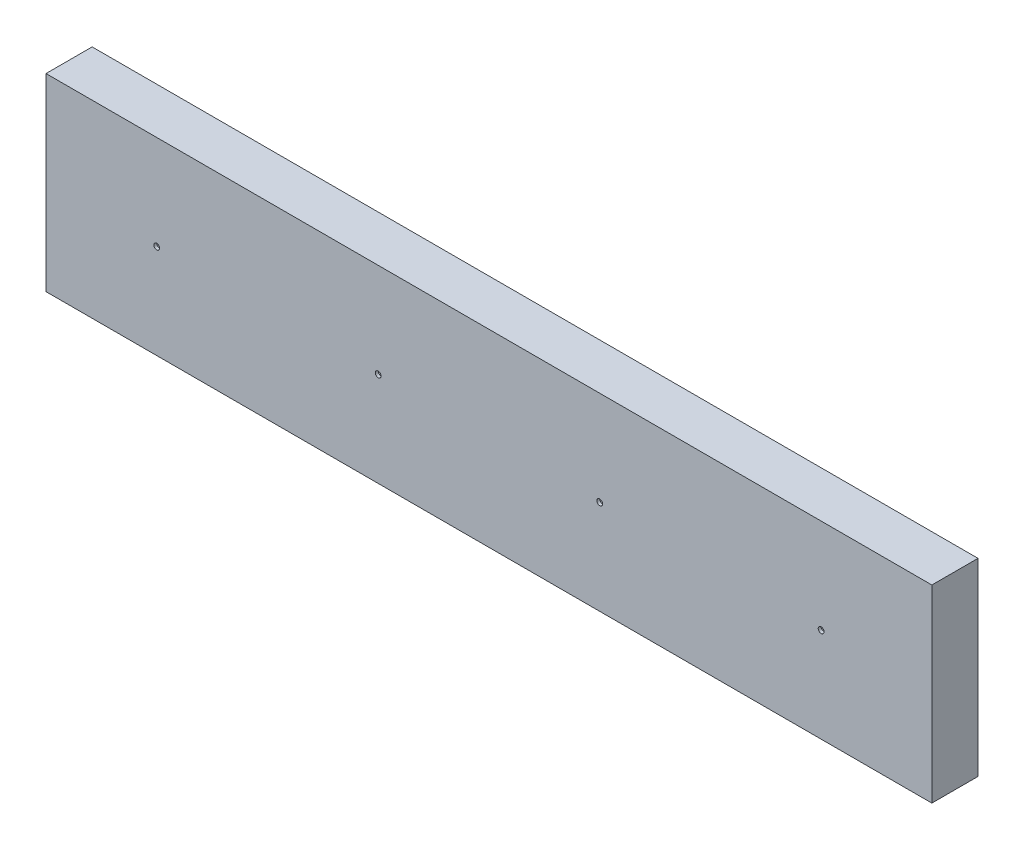
SolidWorks part; units mm, degrees
ref_plane "Front Plane" through (0, 0, 0) normal (0, 0, 1) x (1, 0, 0)
ref_plane "Top Plane" through (0, 0, 0) normal (0, 1, 0) x (1, 0, 0)
ref_plane "Right Plane" through (0, 0, 0) normal (1, 0, 0) x (0, 0, -1)
sketch "Sketch1" plane through (0, 0, 0) normal (0, 0, 1) x (1, 0, 0)
  line L1 (-152.4, 32.5) -> (152.4, 32.5)
  line L2 (-152.4, 32.5) -> (-152.4, -32.5)
  line L3 (-152.4, -32.5) -> (152.4, -32.5)
  line L4 (152.4, 32.5) -> (152.4, -32.5)
  line L5 (-152.4, 32.5) -> (152.4, -32.5) construction
  line L6 (-152.4, -32.5) -> (152.4, 32.5) construction
  point P0 (0, 0)
  dimension "D1" = 65
  dimension "D2" = 304.8
extrude "Boss-Extrude1" add sketch "Sketch1" along normal blind 15.875
sketch "Sketch2" plane through (0, 0, 15.875) normal (0, 0, 1) x (1, 0, 0)
  line L0 (0, 0) -> (0, -32.5) construction
  line L1 (-152.4, -32.5) -> (152.4, -32.5) construction
  circle A0 centre (-38.1, 0) radius 1
  circle A1 centre (-114.3, 0) radius 1
  circle A4 centre (114.3, 0) radius 1
  circle A5 centre (38.1, 0) radius 1
  dimension "D2" = 76.2
  dimension "D3" = 2
  dimension "D1" = 76.2
extrude "Cut-Extrude1" cut sketch "Sketch2" against normal blind 1 and the other way through all
